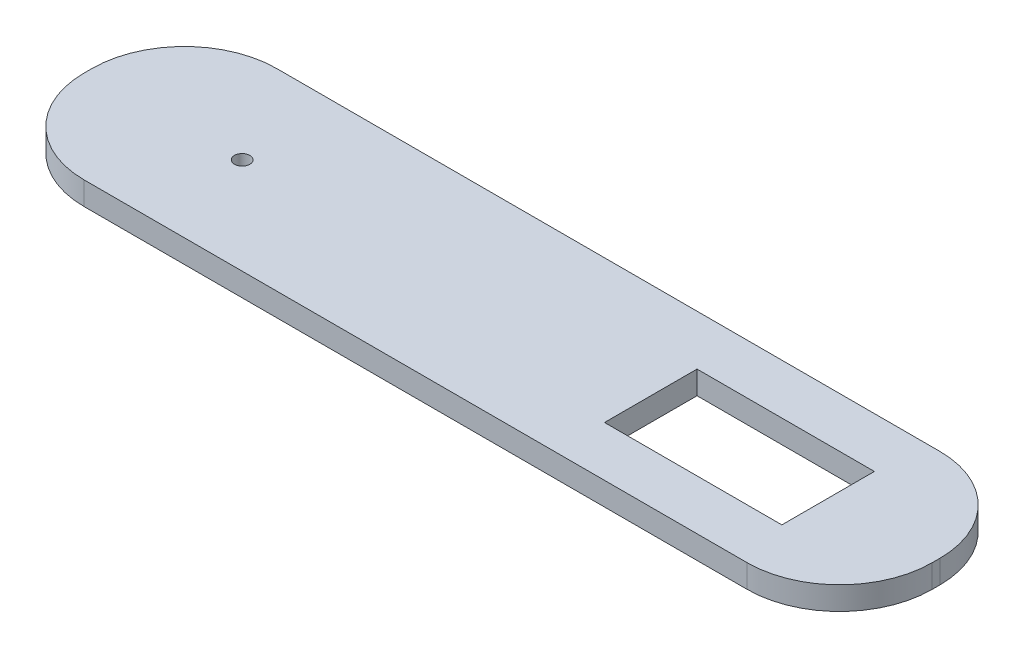
SolidWorks part; units mm, degrees
ref_plane "Front Plane" through (0, 0, 0) normal (0, 0, 1) x (1, 0, 0)
ref_plane "Top Plane" through (0, 0, 0) normal (0, 1, 0) x (1, 0, 0)
ref_plane "Right Plane" through (0, 0, 0) normal (1, 0, 0) x (0, 0, -1)
sketch "Sketch1" plane through (0, 0, 0) normal (0, 1, 0) x (1, 0, 0)
  line L1 (0, 0) -> (110, 0)
  line L2 (0, 0) -> (0, 25)
  line L3 (0, 25) -> (110, 25)
  line L4 (110, 0) -> (110, 25)
  dimension "D1" = 110
  dimension "D2" = 25
extrude "Boss-Extrude1" add sketch "Sketch1" along normal blind 3
sketch "Sketch2" plane through (0, 3, 0) normal (0, 1, 0) x (1, 0, 0)
  line L0 (110, 0) -> (110, 25) construction
  line L1 (73, 18.5) -> (96, 18.5)
  line L2 (73, 18.5) -> (73, 6.5)
  line L3 (73, 6.5) -> (96, 6.5)
  line L4 (96, 18.5) -> (96, 6.5)
  line L5 (110, 25) -> (0, 25) construction
  dimension "D1" = 12
  dimension "D2" = 23
  dimension "D3" = 14
  dimension "D4" = 6.5
extrude "Cut-Extrude1" cut sketch "Sketch2" against normal through all
sketch "Sketch3" plane through (0, 3, 0) normal (0, 1, 0) x (1, 0, 0)
  line L0 (110, 25) -> (0, 25) construction
  line L1 (0, 25) -> (0, 0) construction
  circle A0 centre (20, 12.5) radius 1
  dimension "D1" = 2
  dimension "D2" = 12.5
  dimension "D3" = 20
extrude "Cut-Extrude2" cut sketch "Sketch3" against normal through all
fillet "Fillet1" radius 12 4 edges at (110, 1.5, -25) (110, 1.5, 0) (0, 1.5, -25) (0, 1.5, 0)
